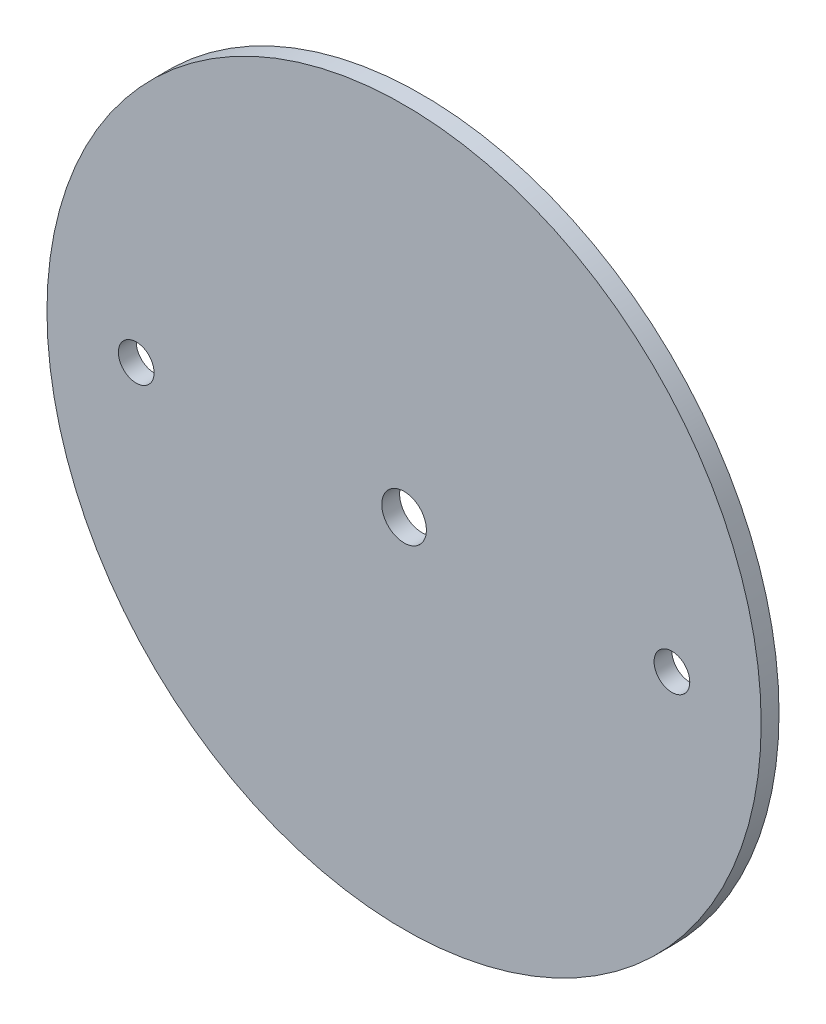
SolidWorks part; units mm, degrees
ref_plane "Front Plane" through (0, 0, 0) normal (0, 0, 1) x (1, 0, 0)
ref_plane "Top Plane" through (0, 0, 0) normal (0, 1, 0) x (1, 0, 0)
ref_plane "Right Plane" through (0, 0, 0) normal (1, 0, 0) x (0, 0, -1)
sketch "Sketch1" plane through (0, 0, 0) normal (0, 0, 1) x (1, 0, 0)
  circle A0 centre (0, 0) radius 63.5
  dimension "D1" = 127
extrude "Boss-Extrude1" add sketch "Sketch1" along normal mid plane 3.175
sketch "Sketch2" plane through (0, 0, 1.5875) normal (0, 0, 1) x (1, 0, 0)
  line L0 (-1000, 0) -> (49000, 0) construction
  line L1 (0, -1000) -> (0, 49000) construction
  point P4 (47.625, 0)
  point P5 (-47.625, 0)
  dimension "D2" = 95.25
  dimension "D1" = 47.625
hole_wizard "1/4 (0.25) Diameter Hole1" positions "Sketch2" profile "Sketch3" hole size "1/4" standard "ANSI Inch" end condition through all
sketch "Sketch3" plane through (-47.625, 0, 1.5875) normal (1, 0, 0) x (0, -1, 0)
  line L0 (0, 0) -> (0, 3.175)
  line L1 (0, 3.175) -> (3.175, 3.175)
  line L2 (3.175, 3.175) -> (3.175, 0)
  line L5 (3.175, 0) -> (0, 0)
  line L11 (0, -6.35) -> (0, 107.95) construction
  dimension "Thru Hole Dia." = 6.35
  dimension "Thru Hole Depth" = 3.175
sketch "Sketch4" plane through (0, 0, 1.5875) normal (0, 0, 1) x (1, 0, 0)
  point P0 (0, 0)
hole_wizard "5/16 (0.3125) Diameter Hole1" positions "Sketch4" profile "Sketch5" hole size "5/16" standard "ANSI Inch"
sketch "Sketch5" plane through (0, 0, 1.5875) normal (1, 0, 0) x (0, -1, 0)
  line L0 (0, 0) -> (0, 3.302)
  line L1 (0, 3.302) -> (3.9687, 3.302)
  line L2 (3.9687, 3.302) -> (3.9688, 0)
  line L5 (3.9688, 0) -> (0, 0)
  line L10 (0, 3.302) -> (-3.9688, 3.302) construction
  line L11 (0, -6.35) -> (0, 107.95) construction
  dimension "Hole Dia." = 7.9375
  dimension "Hole Depth" = 3.302
  dimension "Drill Angle" = 180
equation "\"AIRFRAME_OD\"= 5.15in"
equation "\"AIRFRAME_ID\"= 5.00in"
equation "\"FLAT_T\"= 0.125in"
equation "\"NOSE_EXP_L\"= 27in"
equation "\"NOSE_SHOULDER_L\"= 5in"
equation "\"MAIN_L\"= 30in"
equation "\"RECO_COUP_L\"= 10in"
equation "\"RECO_SWITCH_L\"= 2in"
equation "\"DROGUE_L\"= 20in"
equation "\"ATS_FORE_COUP_L\"= 5.5in"
equation "\"ATS_AFT_COUP_L\"= 4.5in"
equation "\"LOWER_L\"= 30in"
equation "\"FIN_N\"= 4"
equation "\"CR_AFT_X\"= 0.5in"
equation "\"CR_FORE_X\"= 9.25in"
equation "\"FIN_ROOT\"= 8in"
equation "\"FIN_X\"= 0.75in"
equation "\"MOTOR_OD\"= 3.091in"
equation "\"MOTOR_ID\"= 3.00in"
equation "\"COUPLER_OD\"= 4.998in"
equation "\"COUPLER_ID\"= 4.88in"
equation "\"D1@Sketch1\"=\"AIRFRAME_ID\""
equation "\"D1@Boss-Extrude1\"=\"FLAT_T\""
equation "\"RECO_ROD_X\"= 3.5in"
equation "\"ATS_ROD_X\"= 3.75in"
equation "\"D2@Sketch2\"=\"ATS_ROD_X\""
equation "\"MOTOR_L\"= 14in"
equation "\"MOTOR_LOWER_X\"= 2in"
equation "\"D1@Sketch2\"=\"ATS_ROD_X\"/2"
